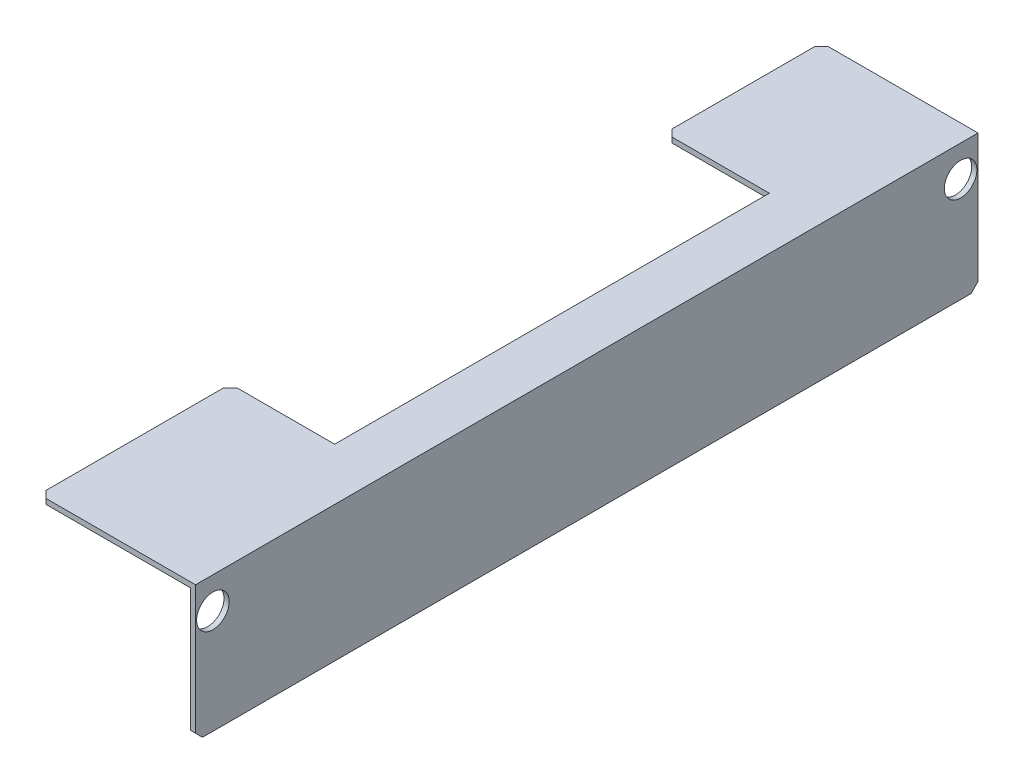
SolidWorks part; units mm, degrees
ref_plane "Front Plane" through (0, 0, 0) normal (0, 0, 1) x (1, 0, 0)
ref_plane "Top Plane" through (0, 0, 0) normal (0, 1, 0) x (1, 0, 0)
ref_plane "Right Plane" through (0, 0, 0) normal (1, 0, 0) x (0, 0, -1)
sketch "Sketch1" plane through (0, 0, 0) normal (0, 0, 1) x (1, 0, 0)
  line L0 (-39.7556, 20.3064) -> (5.2444, 20.3064)
  line L1 (5.2444, 20.3064) -> (5.2444, -18.6936)
  line L2 (5.2444, -18.6936) -> (3.7444, -18.6936)
  line L3 (3.7444, -18.6936) -> (3.7444, 18.8064)
  line L4 (3.7444, 18.8064) -> (-39.7556, 18.8064)
  line L5 (-39.7556, 18.8064) -> (-39.7556, 20.3064)
  dimension "D1" = 45
  dimension "D2" = 39
  dimension "D3" = 1.5
  dimension "D4" = 1.5
extrude "Boss-Extrude1" add sketch "Sketch1" along normal blind 225
sketch "Sketch3" plane through (0, 20.3064, 0) normal (0, 1, 0) x (1, 0, 0)
  line L0 (-39.7556, -225) -> (-39.7556, 0) construction
  line L1 (-39.7556, -45) -> (-9.7556, -45)
  line L2 (-39.7556, -45) -> (-39.7556, -170)
  line L3 (-39.7556, -170) -> (-9.7556, -170)
  line L4 (-9.7556, -45) -> (-9.7556, -170)
  line L5 (5.2444, 0) -> (-39.7556, 0) construction
  dimension "D1" = 30
  dimension "D2" = 125
  dimension "D3" = 45
extrude "Cut-Extrude1" cut sketch "Sketch3" against normal blind 225
sketch "Sketch4" plane through (3.7444, 0, 0) normal (-1, 0, 0) x (0, 0, 1)
  line L0 (45, 20.3064) -> (0, 20.3064) construction
  line L2 (0, 18.8064) -> (0, -18.6936) construction
  circle A0 centre (5, 11.3064) radius 4.6873
  circle A1 centre (220, 11.3064) radius 4.6873
  point P4 (0, 0)
  point P5 (0, 0)
  dimension "D1" = 9
  dimension "D3" = 5
  dimension "D2" = 215
extrude "Cut-Extrude2" cut sketch "Sketch4" against normal blind 225
chamfer "Chamfer1" distance 2 angle 45 6 edges at (-39.7556, 19.5564, 45) (-39.7556, 19.5564, 0) (-39.7556, 19.5564, 170) (-39.7556, 19.5564, 225) (4.4944, -18.6936, 225) (4.4944, -18.6936, 0)
